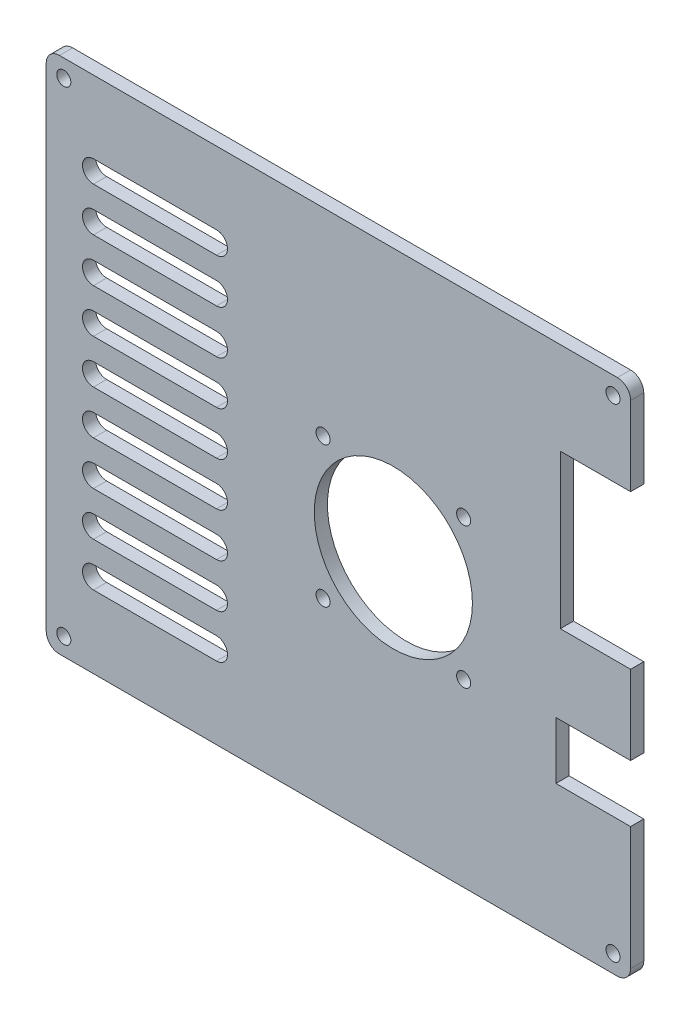
SolidWorks part; units mm, degrees
material "ABS"
ref_plane "Front Plane" through (0, 0, 0) normal (0, 0, 1) x (1, 0, 0)
ref_plane "Top Plane" through (0, 0, 0) normal (0, 1, 0) x (1, 0, 0)
ref_plane "Right Plane" through (0, 0, 0) normal (1, 0, 0) x (0, 0, -1)
sketch "Sketch1" plane through (0, 0, 0) normal (0, 0, 1) x (1, 0, 0)
  line L0 (0, 0) -> (-66.5, 0) construction
  line L1 (-63.5, -59) -> (63.5, -59)
  line L2 (-66.5, -56) -> (-66.5, 56)
  line L3 (-63.5, 59) -> (63.5, 59)
  line L4 (66.5, -56) -> (66.5, -28)
  line L5 (-66.5, -59) -> (66.5, 59) construction
  line L6 (-66.5, 59) -> (66.5, -59) construction
  line L7 (-3.5, -18) -> (28.5, -18) construction
  line L8 (-3.5, -18) -> (-3.5, 14) construction
  line L9 (-3.5, 14) -> (28.5, 14) construction
  line L10 (28.5, -18) -> (28.5, 14) construction
  line L11 (-3.5, -18) -> (28.5, 14) construction
  line L12 (-3.5, 14) -> (28.5, -18) construction
  line L13 (-55.75, 2.5) -> (-27.75, 2.5)
  line L14 (-55.75, -2.5) -> (-27.75, -2.5)
  line L15 (-55.75, 12.5) -> (-27.75, 12.5)
  line L16 (-55.75, 7.5) -> (-27.75, 7.5)
  line L17 (-55.75, 22.5) -> (-27.75, 22.5)
  line L18 (-55.75, 17.5) -> (-27.75, 17.5)
  line L19 (-55.75, 32.5) -> (-27.75, 32.5)
  line L20 (-55.75, 27.5) -> (-27.75, 27.5)
  line L21 (-55.75, 42.5) -> (-27.75, 42.5)
  line L22 (-55.75, 37.5) -> (-27.75, 37.5)
  line L23 (-55.75, -37.5) -> (-27.75, -37.5)
  line L24 (-55.75, -42.5) -> (-27.75, -42.5)
  line L25 (-55.75, -27.5) -> (-27.75, -27.5)
  line L26 (-55.75, -32.5) -> (-27.75, -32.5)
  line L27 (-55.75, -17.5) -> (-27.75, -17.5)
  line L28 (-55.75, -22.5) -> (-27.75, -22.5)
  line L29 (-55.75, -7.5) -> (-27.75, -7.5)
  line L30 (-55.75, -12.5) -> (-27.75, -12.5)
  line L31 (66.5, 38) -> (50.5, 38)
  line L32 (50.5, 38) -> (50.5, 3)
  line L33 (50.5, 3) -> (66.5, 3)
  line L34 (66.5, -15) -> (49.5, -15)
  line L35 (49.5, -15) -> (49.5, -28)
  line L36 (49.5, -28) -> (66.5, -28)
  line L37 (66.5, 38) -> (66.5, 56)
  line L38 (66.5, -15) -> (66.5, 3)
  line L39 (0, 59) -> (0, -59) construction
  circle A0 centre (12.5, -2) radius 18
  circle A1 centre (-3.5, 14) radius 1.6
  circle A2 centre (28.5, 14) radius 1.6
  circle A3 centre (28.5, -18) radius 1.6
  circle A4 centre (-3.5, -18) radius 1.6
  arc A5 (-55.75, 2.5) -> (-55.75, -2.5) centre (-55.75, 0) ccw
  arc A6 (-27.75, -2.5) -> (-27.75, 2.5) centre (-27.75, 0) ccw
  arc A7 (-55.75, 12.5) -> (-55.75, 7.5) centre (-55.75, 10) ccw
  arc A8 (-27.75, 7.5) -> (-27.75, 12.5) centre (-27.75, 10) ccw
  arc A9 (-55.75, 22.5) -> (-55.75, 17.5) centre (-55.75, 20) ccw
  arc A10 (-27.75, 17.5) -> (-27.75, 22.5) centre (-27.75, 20) ccw
  arc A11 (-55.75, 32.5) -> (-55.75, 27.5) centre (-55.75, 30) ccw
  arc A12 (-27.75, 27.5) -> (-27.75, 32.5) centre (-27.75, 30) ccw
  arc A13 (-55.75, 42.5) -> (-55.75, 37.5) centre (-55.75, 40) ccw
  arc A14 (-27.75, 37.5) -> (-27.75, 42.5) centre (-27.75, 40) ccw
  arc A15 (-27.75, -37.5) -> (-27.75, -42.5) centre (-27.75, -40) cw
  arc A16 (-55.75, -42.5) -> (-55.75, -37.5) centre (-55.75, -40) cw
  arc A17 (-27.75, -27.5) -> (-27.75, -32.5) centre (-27.75, -30) cw
  arc A18 (-55.75, -32.5) -> (-55.75, -27.5) centre (-55.75, -30) cw
  arc A19 (-27.75, -17.5) -> (-27.75, -22.5) centre (-27.75, -20) cw
  arc A20 (-55.75, -22.5) -> (-55.75, -17.5) centre (-55.75, -20) cw
  arc A21 (-27.75, -7.5) -> (-27.75, -12.5) centre (-27.75, -10) cw
  arc A22 (-55.75, -12.5) -> (-55.75, -7.5) centre (-55.75, -10) cw
  arc A23 (63.5, 59) -> (66.5, 56) centre (63.5, 56) cw
  arc A24 (66.5, -56) -> (63.5, -59) centre (63.5, -56) cw
  arc A25 (-63.5, -59) -> (-66.5, -56) centre (-63.5, -56) cw
  arc A26 (-66.5, 56) -> (-63.5, 59) centre (-63.5, 56) cw
  circle A27 centre (-62.5, 55) radius 1.6
  circle A28 centre (62.5, 55) radius 1.6
  circle A29 centre (-62.5, -55) radius 1.6
  circle A30 centre (62.5, -55) radius 1.6
  point P0 (0, 0)
  point P22 (12.5, -2)
  dimension "D3" = 54
  dimension "D4" = 61
  dimension "D5" = 36
  dimension "D8" = 3.2
  dimension "D7" = 5
  dimension "D10" = 28
  dimension "D11" = 10.75
  dimension "D13" = 10
  dimension "D19" = 3
  dimension "D20" = 3.2
  dimension "D21" = 125
  dimension "D22" = 110
  dimension "D1" = 133
  dimension "D2" = 118
  dimension "D6" = 32
  dimension "D14" = 21
  dimension "D15" = 35
  dimension "D16" = 16
  dimension "D17" = 18
  dimension "D18" = 13
  dimension "D23" = 17
  dimension "D12" = 5
  dimension "D9" = 4
extrude "Boss-Extrude1" add sketch "Sketch1" along normal blind 3
